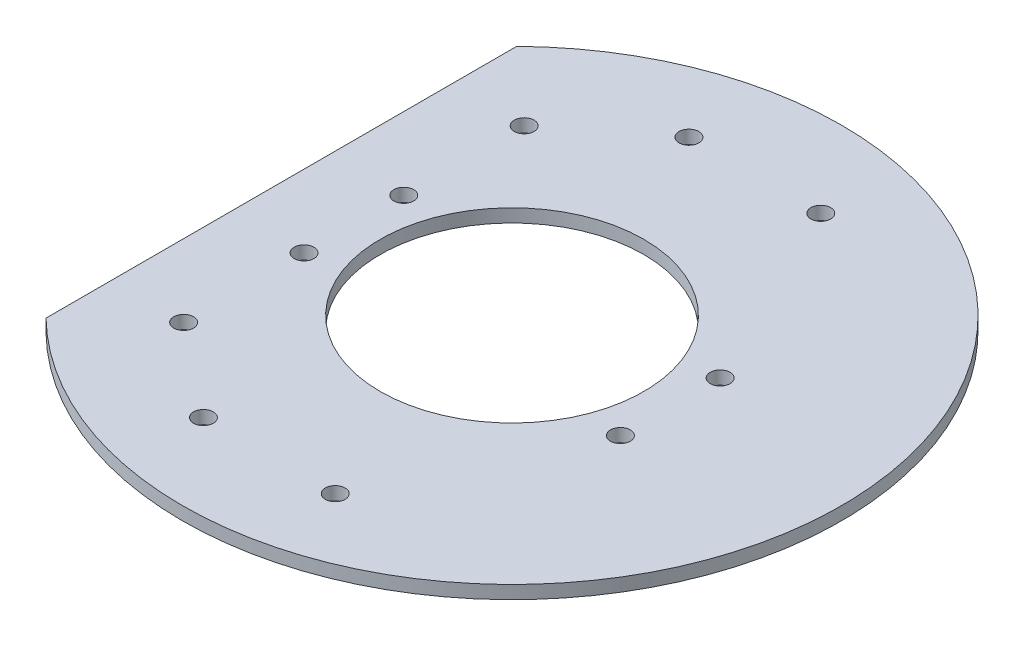
SolidWorks part; units mm, degrees
ref_plane "Front Plane" through (0, 0, 0) normal (0, 0, 1) x (1, 0, 0)
ref_plane "Top Plane" through (0, 0, 0) normal (0, 1, 0) x (1, 0, 0)
ref_plane "Right Plane" through (0, 0, 0) normal (1, 0, 0) x (0, 0, -1)
sketch "Sketch1" plane through (0, 0, 0) normal (0, 1, 0) x (1, 0, 0)
  line L1 (-35, 35.7071) -> (-35, -35.7071)
  arc A0 (-35, -35.7071) -> (-35, 35.7071) centre (0, 0) ccw
  circle A1 centre (0, 0) radius 20
  dimension "D1" = 100
  dimension "D2" = 40
  dimension "D3" = 35
extrude "Boss-Extrude1" add sketch "Sketch1" along normal blind 2
sketch "Sketch2" plane through (0, 2, 0) normal (0, 1, 0) x (1, 0, 0)
  circle A0 centre (-23.9908, 7.5656) radius 1.5
  circle A1 centre (24.0092, 7.5656) radius 1.5
  circle A2 centre (-23.9908, -25.8344) radius 1.5
  circle A3 centre (-9.9908, -36.8344) radius 1.5
  circle A4 centre (10.0092, -36.8344) radius 1.5
  circle A5 centre (0.0092, 0.0656) radius 1
  dimension "D1" = 3
  dimension "D2" = 3
  dimension "D3" = 3
  dimension "D4" = 3
  dimension "D5" = 3
extrude "Cut-Extrude1" cut sketch "Sketch2" against normal blind 2
mirror "Mirror1" about plane through (0, 0, 0) normal (0, 0, 1) of "Cut-Extrude1"
